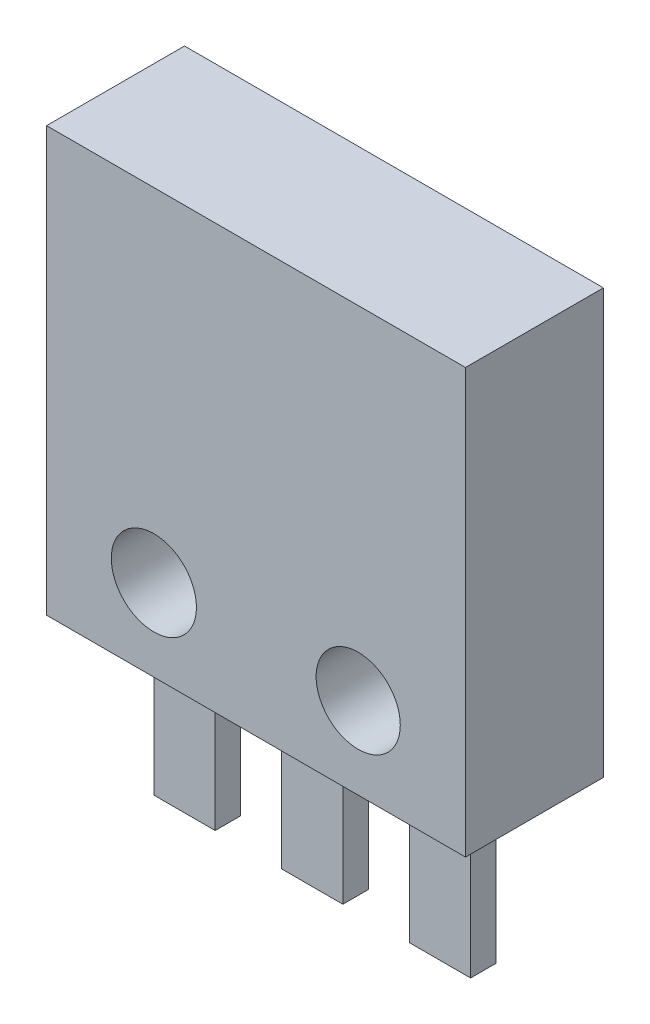
SolidWorks part; units mm, degrees
ref_plane "Front Plane" through (0, 0, 0) normal (0, 0, 1) x (1, 0, 0)
ref_plane "Top Plane" through (0, 0, 0) normal (0, 1, 0) x (1, 0, 0)
ref_plane "Right Plane" through (0, 0, 0) normal (1, 0, 0) x (0, 0, -1)
sketch "Sketch2" plane through (0, 0, 0) normal (0, 0, 1) x (1, 0, 0)
  line L1 (-4.1, 4.15) -> (4.1, 4.15)
  line L2 (-4.1, 4.15) -> (-4.1, -4.15)
  line L3 (-4.1, -4.15) -> (4.1, -4.15)
  line L4 (4.1, 4.15) -> (4.1, -4.15)
  line L5 (-4.1, 4.15) -> (4.1, -4.15) construction
  line L6 (-4.1, -4.15) -> (4.1, 4.15) construction
  circle A0 centre (-2, -2.55) radius 0.8334
  circle A1 centre (2, -2.55) radius 0.8238
  point P0 (0, 0)
  point P10 (0, 0)
  dimension "D1" = 8.2
  dimension "D2" = 8.3
  dimension "D3" = 4
  dimension "D4" = 2
  dimension "D5" = 1.6
extrude "Boss-Extrude1" add sketch "Sketch2" along normal mid plane 2.7
sketch "Sketch3" plane through (0, 0, 0) normal (0, 0, 1) x (1, 0, 0)
  line L0 (-4.1, -4.15) -> (4.1, -4.15) construction
  line L1 (-0.6, -4.15) -> (0.6, -4.15)
  line L2 (-0.6, -4.15) -> (-0.6, -7.25)
  line L3 (-0.6, -7.25) -> (0.6, -7.25)
  line L4 (0.6, -4.15) -> (0.6, -7.25)
  line L5 (1.9, -4.15) -> (3.1, -4.15)
  line L6 (1.9, -4.15) -> (1.9, -7.25)
  line L7 (1.9, -7.25) -> (3.1, -7.25)
  line L8 (3.1, -4.15) -> (3.1, -7.25)
  line L9 (-3.1, -4.15) -> (-1.9, -4.15)
  line L10 (-3.1, -4.15) -> (-3.1, -7.25)
  line L11 (-3.1, -7.25) -> (-1.9, -7.25)
  line L12 (-1.9, -4.15) -> (-1.9, -7.25)
  point P12 (0, -4.15)
  point P14 (-2.5, -7.25)
  point P15 (2.5, -7.25)
  point P16 (0, -7.25)
  point P17 (-3.1, -6.085)
  dimension "D1" = 1.2
  dimension "D2" = 5
  dimension "D3" = 3.1
  dimension "D4" = 2.5
extrude "Boss-Extrude2" add sketch "Sketch3" along normal mid plane 0.5
